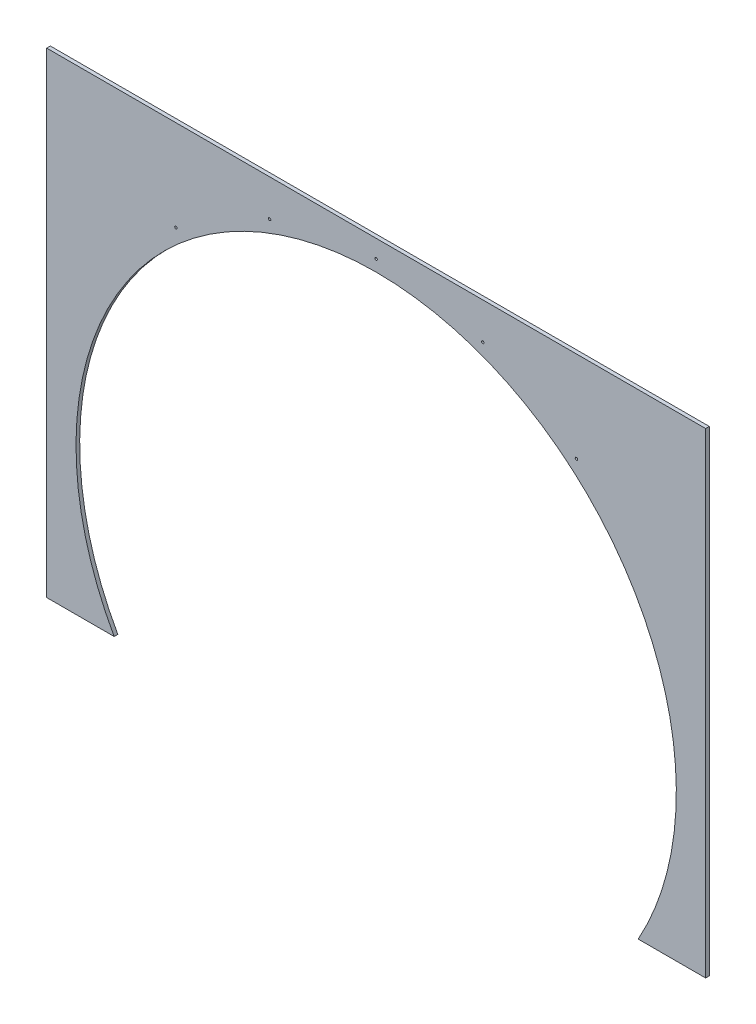
SolidWorks part; units mm, degrees
ref_plane "Plano frontal" through (0, 0, 0) normal (0, 0, 1) x (1, 0, 0)
ref_plane "Plano superior" through (0, 0, 0) normal (0, 1, 0) x (1, 0, 0)
ref_plane "Plano direito" through (0, 0, 0) normal (1, 0, 0) x (0, 0, -1)
sketch "Esboço1" plane through (0, 0, 0) normal (0, 0, 1) x (1, 0, 0)
  line L0 (715.8212, 0) -> (900, 0)
  line L1 (-900, 0) -> (-715.8212, 0)
  line L2 (-900, 0) -> (-900, 1300)
  line L3 (-900, 1300) -> (900, 1300)
  line L4 (900, 0) -> (900, 1300)
  line L5 (-715.8212, 0) -> (715.8212, 0) construction
  arc A0 (715.8212, 0) -> (-715.8212, 0) centre (0, 400) ccw
  point P4 (0, 0)
  point P7 (0, 1300)
  dimension "D1" = 820
  dimension "D3" = 900
  dimension "D2" = 1800
  dimension "D4" = 1300
extrude "Ressalto-extrusão1" add sketch "Esboço1" along normal blind 10
hole_wizard "Furo com folga de M61" positions "Esboço2" profile "Esboço3" hole size "M6" standard "Ansi Metric"
sketch "Esboço2" plane through (0, 400, -6) normal (0, 0, -1) x (-1, 0, 0)
  line L1 (0, 880) -> (0, 822.219) construction
  circle A2 centre (0, 0) radius 851.1095 construction
  point P0 (0, 851.1095)
  point P21 (291.0966, 799.7813)
  point P22 (547.0826, 651.9877)
  point P30 (-291.0966, 799.7813)
  point P31 (-547.0826, 651.9877)
sketch "Esboço3" plane through (0, 1251.1095, -6) normal (1, 0, 0) x (0, 1, 0)
  line L0 (0, 0) -> (0, 17.9818)
  line L1 (0, 17.9818) -> (3.3, 15.999)
  line L2 (3.3, 15.999) -> (3.3, 0)
  line L3 (3.3, 0) -> (0, 0)
  line L4 (0, 17.9818) -> (-3.3, 15.999) construction
  line L5 (0, -6.35) -> (0, 107.95) construction
  dimension "Hole Dia." = 6.6
  dimension "Hole Depth" = 15.999
  dimension "Drill Angle" = 118
